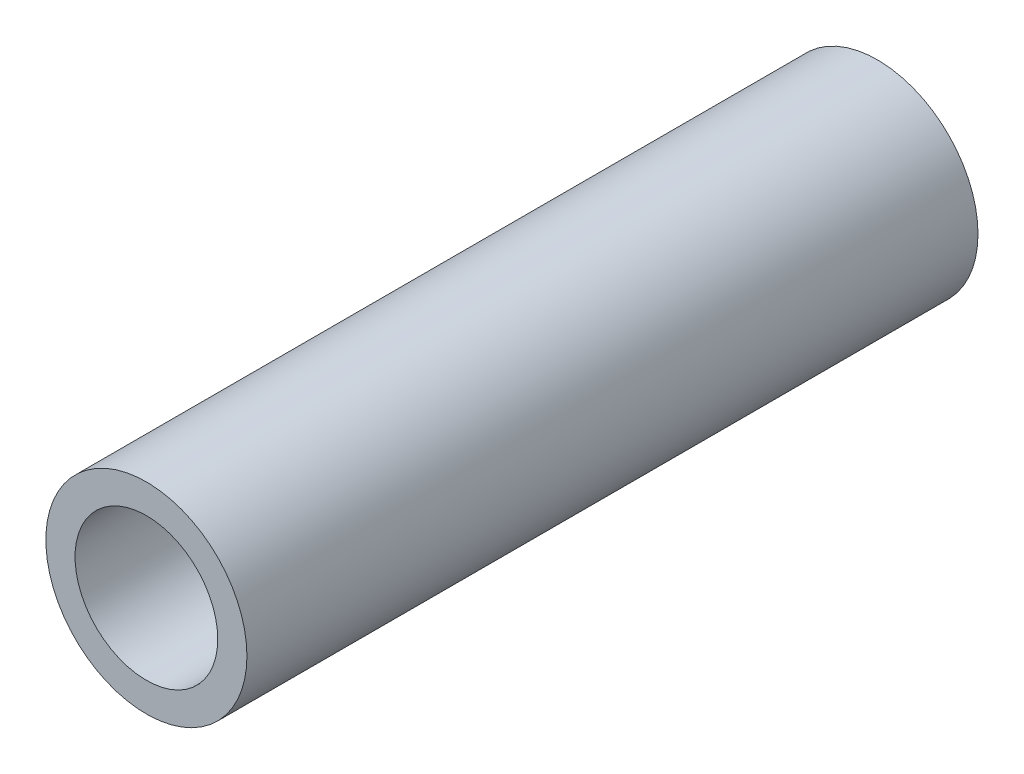
SolidWorks part; units mm, degrees
material "7075-T6 (SN)"
ref_plane "Top" through (0, 0, 0) normal (0, 0, 1) x (1, 0, 0)
ref_plane "Right" through (0, 0, 0) normal (0, 1, 0) x (1, 0, 0)
ref_plane "Front" through (0, 0, 0) normal (1, 0, 0) x (0, 0, -1)
sketch "Sketch1" plane through (0, 0, 0) normal (0, 0, 1) x (1, 0, 0)
  circle A0 centre (0, 0) radius 2.794
  circle A1 centre (0, 0) radius 3.937
  dimension "D1" = 5.588
  dimension "D2" = 7.874
extrude "Boss-Extrude1" add sketch "Sketch1" along normal blind 28.6258
